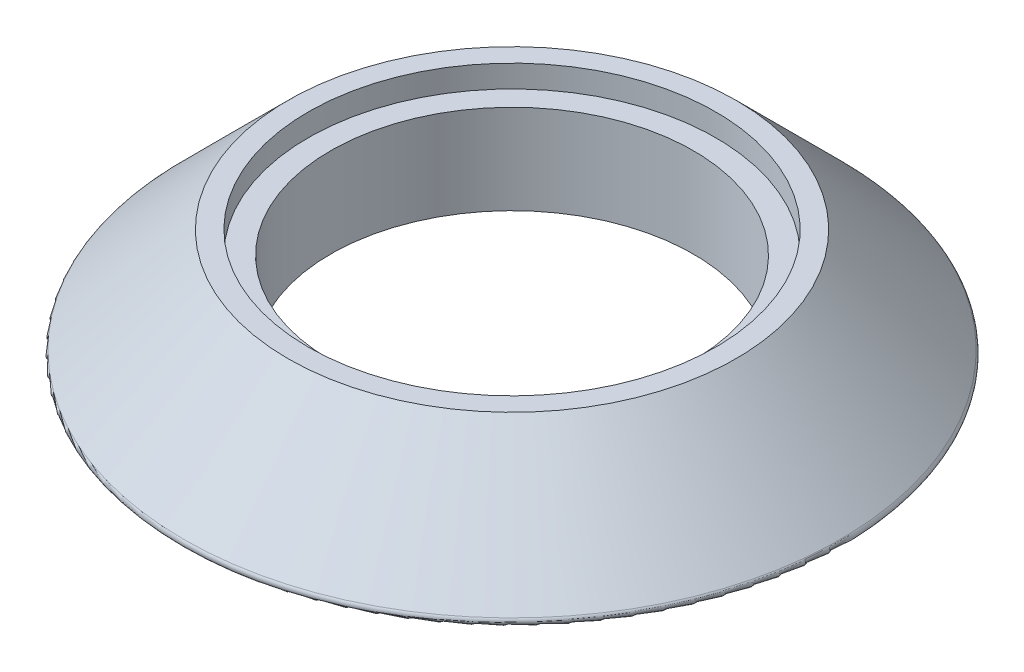
SolidWorks part; units mm, degrees
material "ABS"
ref_plane "前视基准面" through (0, 0, 0) normal (0, 0, 1) x (1, 0, 0)
ref_plane "上视基准面" through (0, 0, 0) normal (0, 1, 0) x (1, 0, 0)
ref_plane "右视基准面" through (0, 0, 0) normal (1, 0, 0) x (0, 0, -1)
sketch "草图1" plane through (0, 0, 0) normal (0, 1, 0) x (1, 0, 0)
  circle A0 centre (0, 0) radius 10
  circle A1 centre (0, 0) radius 8.1
  dimension "D1" = 16.2
  dimension "D2" = 20
extrude "凸台-拉伸1" add sketch "草图1" along normal blind 5
sketch "草图2" plane through (0, 0, 0) normal (1, 0, 0) x (0, 0, -1)
  line L0 (10, 5) -> (10, 0)
  line L1 (10, 0) -> (15, 0)
  line L2 (15, 0) -> (10, 5)
  line L3 (0, 0) -> (0, 5) construction
  line L4 (10, 5) -> (-10, 5) construction
  line L5 (-10, 0) -> (10, 0) construction
  dimension "D1" = 5
  dimension "D2" = 5
  dimension "D3" = 10
revolve "旋转1" add sketch "草图2" angle 360 about L3
fillet "圆角1" radius 0.2 1 edges at (0, 0, -15)
sketch "草图3" plane through (0, 5, 0) normal (0, 1, 0) x (1, 0, 0)
  circle A0 centre (0, 0) radius 9.1
  dimension "D1" = 18.2
extrude "切除-拉伸1" cut sketch "草图3" against normal blind 1
